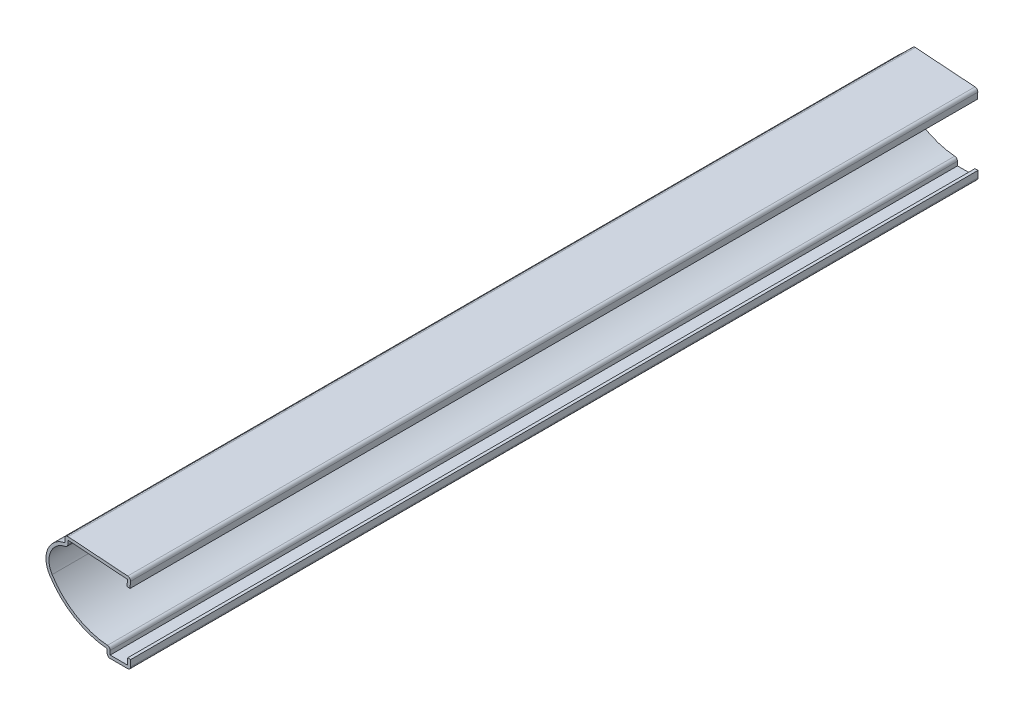
SolidWorks part; units mm, degrees
ref_plane "Front Plane" through (0, 0, 0) normal (0, 0, 1) x (1, 0, 0)
ref_plane "Top Plane" through (0, 0, 0) normal (0, 1, 0) x (1, 0, 0)
ref_plane "Right Plane" through (0, 0, 0) normal (1, 0, 0) x (0, 0, -1)
sketch "Sketch1" plane through (0, 0, 0) normal (0, 0, 1) x (1, 0, 0)
  line L0 (0, 3.175) -> (0, 0)
  line L1 (0, 0) -> (-7.9375, 0)
  line L2 (-7.9375, 0) -> (-7.9375, 2.3812)
  line L3 (-22.225, 26.1937) -> (-22.225, 28.575)
  line L4 (-22.225, 28.575) -> (0, 26.9875)
  line L5 (0, 26.9875) -> (-0.2268, 23.8125)
  arc A0 (-7.9375, 2.3812) -> (-27.3619, 14.1993) centre (-5.8438, 27.6948) cw
  arc A1 (-27.3619, 14.1993) -> (-22.225, 26.1937) centre (-20.6375, 18.4166) cw
  point P9 (0, 0)
  point P13 (-0.1395, 26.9875)
  dimension "D7" = 7.9375
  dimension "D8" = 25.4
  dimension "D1" = 28.575
  dimension "D2" = 28.575
  dimension "D3" = 3.175
  dimension "D4" = 1.5875
  dimension "D5" = 2.3813
  dimension "D6" = 6.35
  dimension "D9" = 2.3813
  dimension "D10" = 3.175
  dimension "D11" = 7.9375
extrude "Extrude-Thin1" add sketch "Sketch1" against normal blind 285.75 thin
fillet "Fillet1" radius 1.016 6 edges at (0, 0, -142.875) (-7.9375, 0, -142.875) (-6.9215, 3.3346, -142.875) (-21.209, 25.3145, -142.875) (0, 26.9875, -142.875) (-22.225, 28.575, -142.875)
